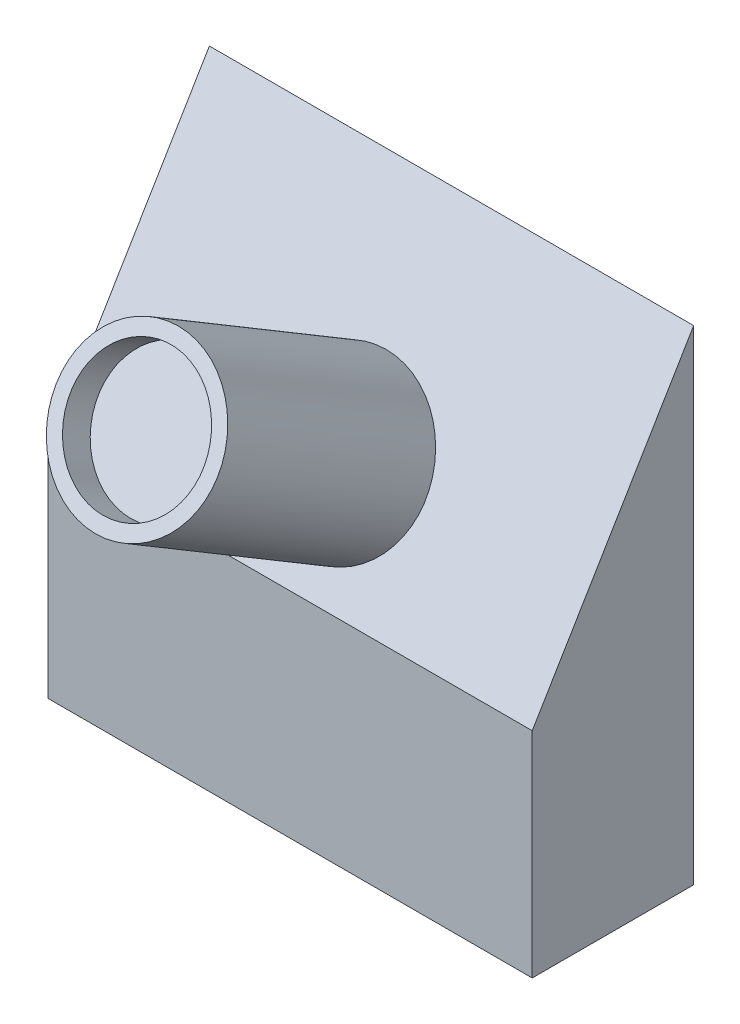
SolidWorks part; units mm, degrees
ref_plane "Front Plane" through (0, 0, 0) normal (0, 0, 1) x (1, 0, 0)
ref_plane "Top Plane" through (0, 0, 0) normal (0, 1, 0) x (1, 0, 0)
ref_plane "Right Plane" through (0, 0, 0) normal (1, 0, 0) x (0, 0, -1)
sketch "Sketch2" plane through (0, 0, 0) normal (0, 0, 1) x (1, 0, 0)
  line L1 (-15, 15) -> (15, 15)
  line L2 (-15, 15) -> (-15, -15)
  line L3 (-15, -15) -> (15, -15)
  line L4 (15, 15) -> (15, -15)
  line L5 (-15, 15) -> (15, -15) construction
  line L6 (-15, -15) -> (15, 15) construction
  point P0 (0, 0)
  dimension "D1" = 30
  dimension "D2" = 30
extrude "Boss-Extrude2" add sketch "Sketch2" along normal blind 10
sketch "Sketch5" plane through (15, 0, 0) normal (1, 0, 0) x (0, 0, -1)
  line L0 (0, 15) -> (-10, -1.7337)
  line L1 (-10, -15) -> (-10, 15) construction
  line L2 (-10, -1.7337) -> (-10, 15)
  line L3 (-10, 15) -> (0, 15)
extrude "Cut-Extrude2" cut sketch "Sketch5" against normal blind 36
sketch "Sketch6" plane through (0, 3.9472, 6.6051) normal (0, 0.513, 0.8584) x (1, 0, 0)
  circle A0 centre (0, 0) radius 5
  dimension "D1" = 10
extrude "Boss-Extrude3" add sketch "Sketch6" along normal blind 15
sketch "Sketch7" plane through (0, 11.6418, 19.4811) normal (0, 0.513, 0.8584) x (1, 0, 0)
  circle A0 centre (0, 0) radius 4.1099
extrude "Cut-Extrude3" cut sketch "Sketch7" against normal blind 2
